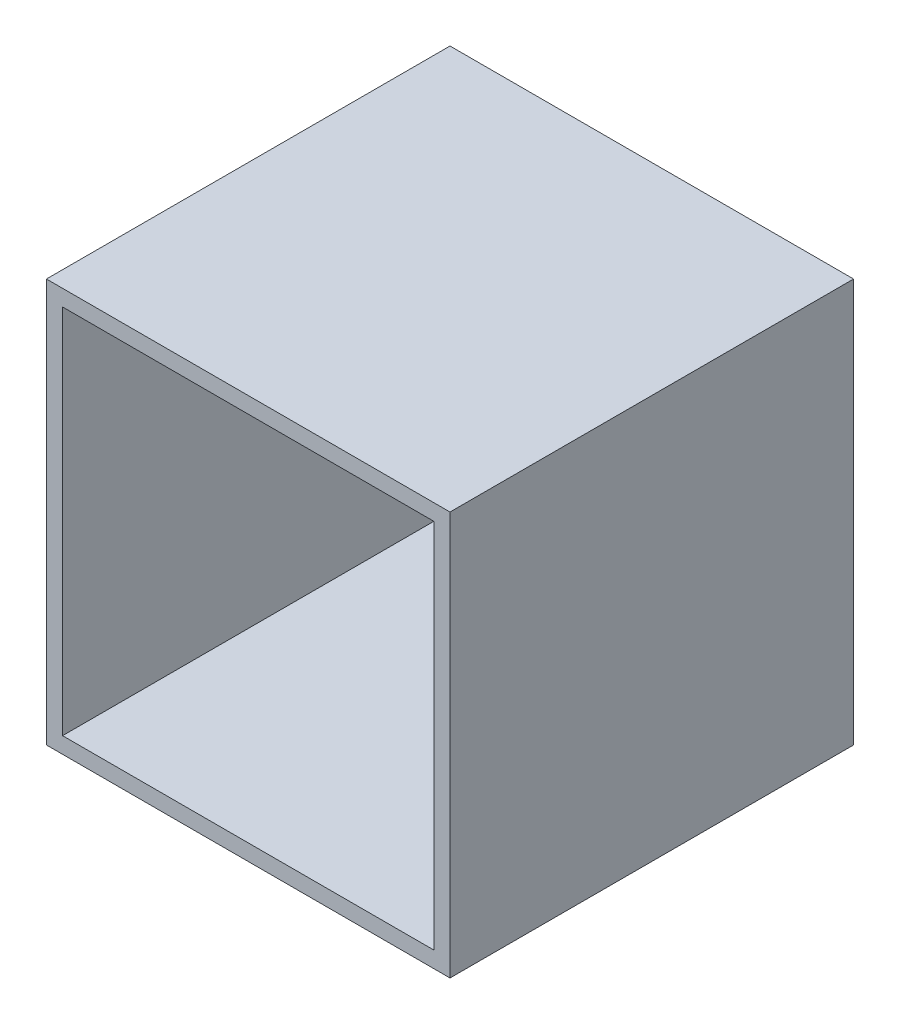
SolidWorks part; units mm, degrees
ref_plane "Front" through (0, 0, 0) normal (0, 0, 1) x (1, 0, 0)
ref_plane "Top" through (0, 0, 0) normal (0, 1, 0) x (1, 0, 0)
ref_plane "Right" through (0, 0, 0) normal (1, 0, 0) x (0, 0, -1)
sketch "Sketch1" plane through (0, 0, 0) normal (0, 0, 1) x (1, 0, 0)
  line L0 (0, 0) -> (0, 36.4553) construction
  line L1 (-5, 5) -> (5, 5)
  line L2 (-5, 5) -> (-5, -5)
  line L3 (-5, -5) -> (5, -5)
  line L4 (5, 5) -> (5, -5)
  line L5 (0, 0) -> (43.2883, 0) construction
  point P5 (0, 5)
  point P10 (5, 0)
  dimension "D1" = 10
  dimension "D2" = 10
extrude "Boss-Extrude1" add sketch "Sketch1" along normal blind 0.4
sketch "Sketch2" plane through (0, 0, 0.4) normal (0, 0, 1) x (1, 0, 0)
  line L1 (-5, 5) -> (5, 5)
  line L2 (-5, 5) -> (-5, -5)
  line L3 (-5, -5) -> (5, -5)
  line L4 (5, 5) -> (5, -5)
  line L5 (-4.6, 4.6) -> (4.6, 4.6)
  line L6 (-4.6, 4.6) -> (-4.6, -4.6)
  line L7 (-4.6, -4.6) -> (4.6, -4.6)
  line L8 (4.6, 4.6) -> (4.6, -4.6)
  dimension "D1" = 0.4
  dimension "D2" = 0.4
  dimension "D3" = 0.4
  dimension "D4" = 0.4
extrude "Boss-Extrude2" add sketch "Sketch2" along normal blind 9.6
